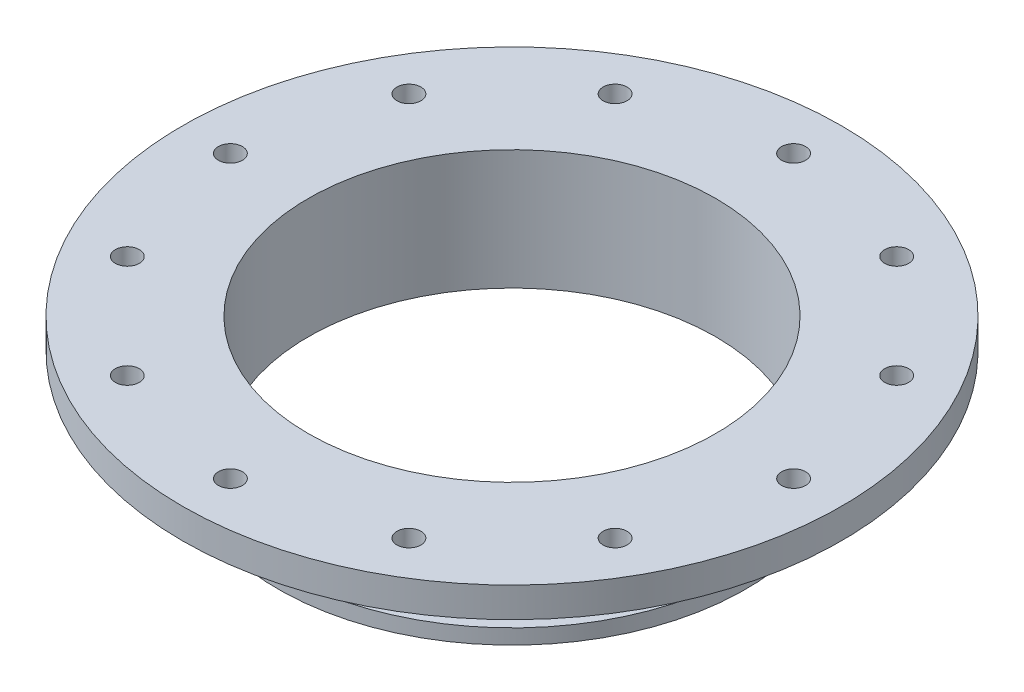
SolidWorks part; units mm, degrees
material "1023 Carbon Steel Sheet (SS)"
ref_plane "Front Plane" through (0, 0, 0) normal (0, 0, 1) x (1, 0, 0)
ref_plane "Top Plane" through (0, 0, 0) normal (0, 1, 0) x (1, 0, 0)
ref_plane "Right Plane" through (0, 0, 0) normal (1, 0, 0) x (0, 0, -1)
sketch "Sketch1" plane through (0, 0, 0) normal (0, 0, 1) x (1, 0, 0)
  line L0 (-43.18, 0) -> (43.18, 0) construction
  line L1 (0, -127) -> (0, 127) construction
  line L2 (43.18, 0) -> (43.18, -6.35)
  line L4 (43.18, 0) -> (69.85, 0)
  line L6 (43.18, -6.35) -> (69.85, -6.35)
  line L7 (69.85, -6.35) -> (69.85, 0)
  point P4 (0, 0)
  point P8 (0, 0)
  dimension "D1" = 86.36
  dimension "D2" = 254
  dimension "D3" = 6.35
  dimension "D4" = 26.67
revolve "Revolve1" add sketch "Sketch1" angle 360 about L1
sketch "Sketch2" plane through (0, -6.35, 0) normal (0, -1, 0) x (1, 0, 0)
  circle A0 centre (0, 0) radius 43.18
  circle A1 centre (0, 0) radius 43.18 construction
  circle A2 centre (0, 0) radius 49.53
  dimension "D1" = 6.35
extrude "Boss-Extrude1" add sketch "Sketch2" along normal blind 19.05
sketch "Sketch3" plane through (0, 0, 0) normal (0, 0, 1) x (1, 0, 0)
  line L0 (0, 0) -> (0, -37.1244) construction
  line L1 (49.53, -25.4) -> (49.53, -6.35) construction
  line L2 (-49.53, -25.4) -> (49.53, -25.4) construction
  line L3 (-49.53, -6.35) -> (49.53, -6.35) construction
  line L5 (49.53, -25.4) -> (46.355, -25.4)
  line L6 (49.53, -25.4) -> (49.53, -6.35) construction
  line L7 (49.53, -6.35) -> (46.355, -6.35)
  line L8 (46.355, -25.4) -> (46.355, -6.35)
  line L9 (49.53, -22.225) -> (46.355, -22.225)
  line L10 (49.53, -22.225) -> (49.53, -20.1083)
  line L11 (49.53, -20.1083) -> (46.355, -20.1083)
  line L12 (46.355, -22.225) -> (46.355, -20.1083)
  line L13 (49.53, -16.9333) -> (46.355, -16.9333)
  line L14 (49.53, -16.9333) -> (49.53, -14.8167)
  line L15 (49.53, -14.8167) -> (46.355, -14.8167)
  line L16 (46.355, -16.9333) -> (46.355, -14.8167)
  line L17 (49.53, -11.6417) -> (46.355, -11.6417)
  line L18 (49.53, -11.6417) -> (49.53, -9.525)
  line L19 (49.53, -9.525) -> (46.355, -9.525)
  line L20 (46.355, -11.6417) -> (46.355, -9.525)
  dimension "D1" = 3.175
  dimension "D2" = 3.175
  dimension "D3" = 3.175
  dimension "D4" = 3.175
  dimension "D5" = 3.175
revolve "Cut-Revolve1" cut sketch "Sketch3" angle 360 about L0
sketch "Sketch4" plane through (0, 0, 0) normal (0, 1, 0) x (1, 0, 0)
  line L0 (0, 0) -> (-49.53, 0)
  line L1 (-49.53, 0) -> (-59.69, 0)
  circle A0 centre (0, 0) radius 49.53 construction
  circle A1 centre (-59.69, 0) radius 2.54
  dimension "D2" = 5.08
  dimension "D1" = 10.16
extrude "Cut-Extrude1" cut sketch "Sketch4" against normal through all
pattern_circular "CirPattern1" count 12 over 360 about axis through (0, 0, 0) along (0, 1, 0) of "Cut-Extrude1"
sketch "point" plane through (0, 0, 0) normal (0, 1, 0) x (1, 0, 0)
  point P0 (0, 0)
equation "\"D3@Sketch3\"=\"D2@Sketch3\""
equation "\"D4@Sketch3\"=\"D2@Sketch3\""
equation "\"D5@Sketch3\"=\"D2@Sketch3\""
